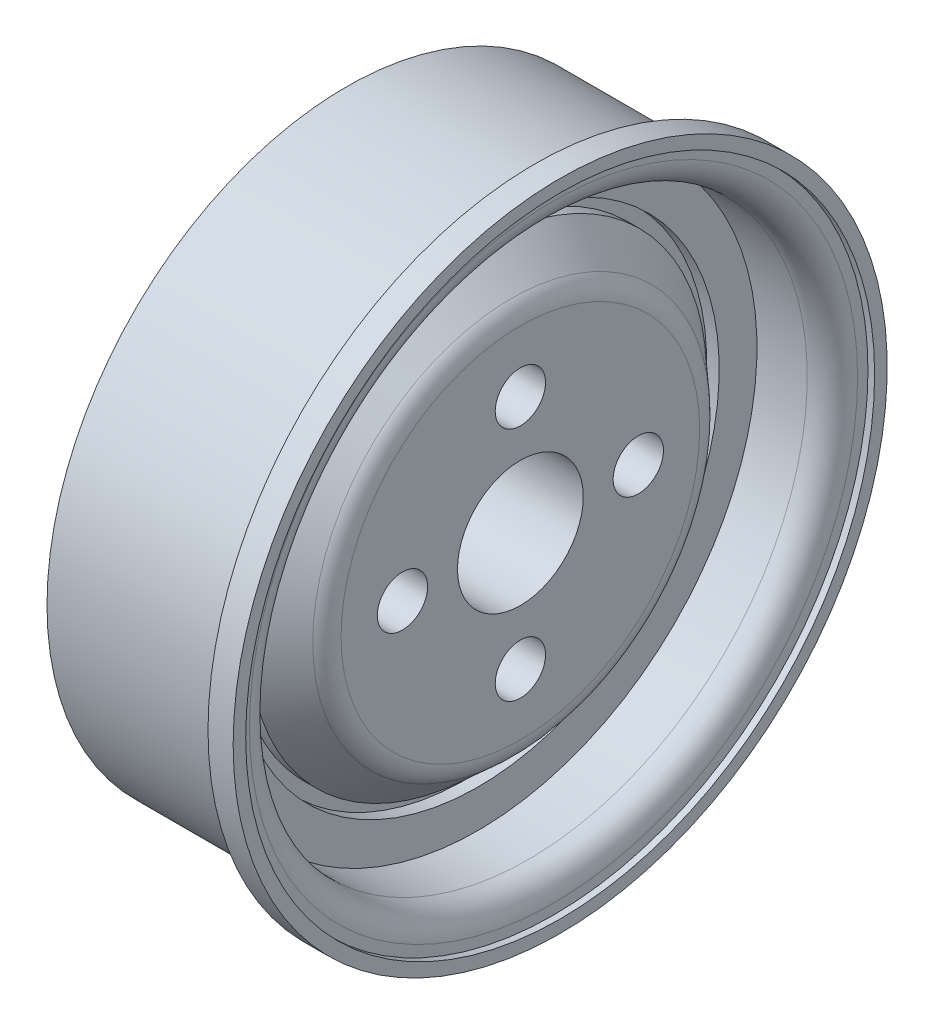
SolidWorks part; units mm, degrees
ref_plane "Front Plane" through (0, 0, 0) normal (0, 0, 1) x (1, 0, 0)
ref_plane "Top Plane" through (0, 0, 0) normal (0, 1, 0) x (1, 0, 0)
ref_plane "Right Plane" through (0, 0, 0) normal (1, 0, 0) x (0, 0, -1)
sketch "Sketch1" plane through (0, 0, 0) normal (0, 1, 0) x (1, 0, 0)
  line L0 (-7.1397, 0) -> (9.2571, 0) construction
  line L1 (5.4294, 13) -> (4.4294, 13)
  line L2 (4.4294, 13) -> (4.4294, 11.9)
  line L7 (5.1646, 12.5) -> (5.4294, 12.5)
  line L8 (5.4294, 12.5) -> (5.4294, 13)
  line L9 (5.1646, 12.5) -> (5.1646, 11.0868)
  line L10 (5.1646, 11.0868) -> (2.1646, 11.0868)
  line L11 (2.1646, 11.0868) -> (2.1646, 9.5868)
  line L13 (3.8471, 7.1283) -> (3.8471, 0)
  line L17 (4.4294, 11.9) -> (-3.0706, 11.9)
  line L26 (0.1646, 9.9) -> (0.1646, 7.0868)
  line L27 (0.1646, 9.9) -> (0.1646, 9.9)
  line L28 (0.1646, 9.9) -> (0.1646, 9.9)
  line L29 (0.1646, 9.9) -> (0.1646, 9.9)
  line L30 (0.1646, 9.9) -> (0.1646, 9.9)
  line L31 (0.1646, 9.9) -> (0.1646, 9.9)
  line L32 (0.1646, 9.9) -> (0.1646, 9.9)
  line L33 (0.1646, 9.9) -> (-3.0706, 9.9)
  line L35 (-3.0706, 11.9) -> (-3.0706, 9.9)
  line L36 (0, 2) -> (1.8471, 2) construction
  line L37 (0, 0) -> (3.8471, 0) construction
  line L38 (-3.9543, 2) -> (0, 2) construction
  line L39 (-3.9543, 0) -> (0, 0) construction
  line L40 (1.8471, 1.25) -> (1.8471, 0)
  line L41 (1.8471, 0) -> (3.8471, 0)
  line L42 (0.1646, 7.0868) -> (1.3408, 7.0868) construction
  line L43 (1.3408, 7.0868) -> (1.8471, 6.662) construction
  line L44 (1.8471, 6.662) -> (1.8471, 2) construction
  line L45 (1.3408, 7.0868) -> (1.3408, 7.0868) construction
  line L46 (0.1646, 7.0868) -> (0.1646, 3.25)
  line L47 (0.1646, 3.25) -> (-4.8354, 3.25)
  line L48 (-4.8354, 3.25) -> (-4.8354, 1.25)
  line L49 (-4.8354, 1.25) -> (1.8471, 1.25)
  line L50 (2.1646, 9.0868) -> (3.4899, 7.8943)
  line L51 (2.1646, 9.0868) -> (2.6646, 9.0868) construction
  line L52 (2.6646, 9.0868) -> (2.6646, 8.5868) construction
  line L53 (2.1646, 9.5868) -> (1.6646, 9.5868)
  line L54 (2.6646, 8.5868) -> (3.4899, 7.8943) construction
  line L55 (1.6646, 9.5868) -> (1.6646, 9.0868)
  line L56 (1.6646, 9.0868) -> (2.1646, 9.0868)
  line L58 (2.1646, 11.0868) -> (2.1646, 9.0868) construction
  arc A0 (3.4899, 7.8943) -> (3.8471, 7.1283) centre (2.8471, 7.1283) cw
  arc A2 (1.8471, 6.662) -> (1.8471, 6.662) centre (1.8471, 6.662) cw construction
  point P19 (4.4294, 12.45)
  dimension "D12" = 1
  dimension "D1" = 0.5
  dimension "D2" = 26
  dimension "D3" = 7.5
  dimension "D4" = 1
  dimension "D5" = 1.1
  dimension "D6" = 2
  dimension "D7" = 5
  dimension "D8" = 0.7352
  dimension "D9" = 2
  dimension "D10" = 8.5
  dimension "D11" = 8.2352
  dimension "D13" = 3
  dimension "D14" = 2
  dimension "D15" = 2.5
  dimension "D16" = 0.5
  dimension "D17" = 23.8
  dimension "D18" = 0.5
  dimension "D19" = 1.5
revolve "Revolve1" add sketch "Sketch1" angle 360 about L0
fillet "Fillet1" radius 1 1 edges at (5.1646, 0, 11.0868)
sketch "Sketch2" plane through (3.8471, 0, 0) normal (1, 0, 0) x (0, 0, -1)
  circle A0 centre (0, 0) radius 2.5
  circle A1 centre (0, 0) radius 4.6872 construction
  circle A2 centre (0, 4.6872) radius 1
  circle A3 centre (4.6872, 0) radius 1
  circle A4 centre (0, -4.6872) radius 1
  circle A5 centre (-4.6872, 0) radius 1
  point P15 (0, 0)
  dimension "D1" = 5
  dimension "D3" = 2
  dimension "D2" = 4
extrude "Cut-Extrude1" cut sketch "Sketch2" against normal mid plane 10
